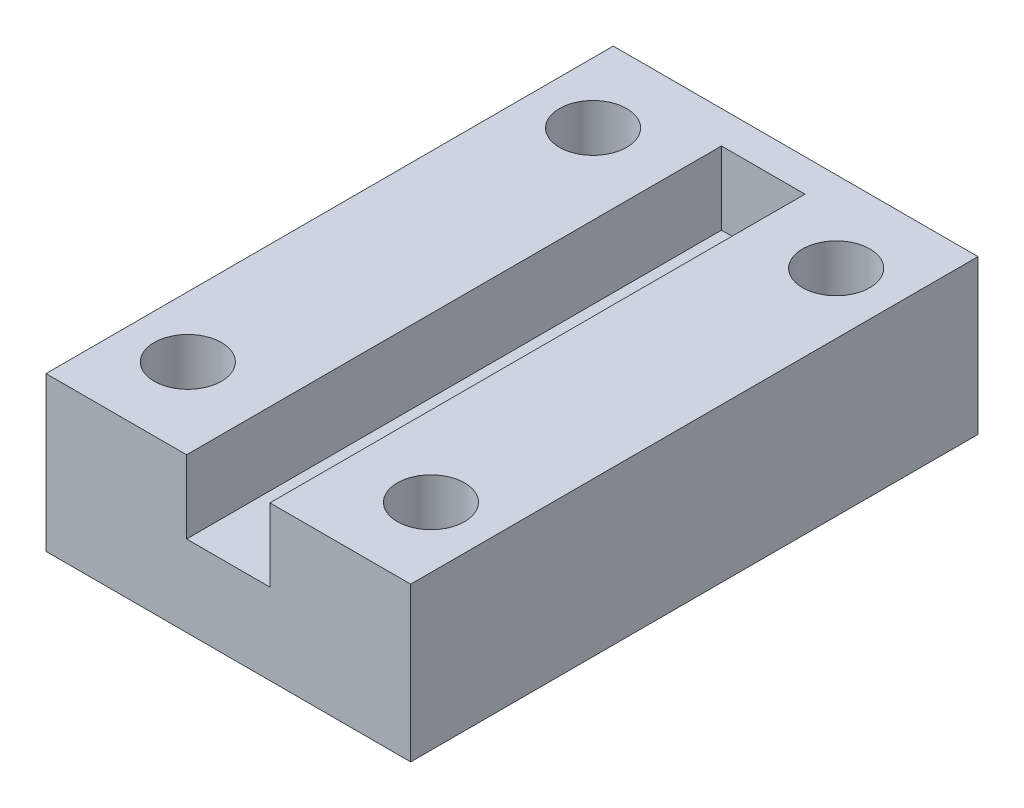
SolidWorks part; units mm, degrees
ref_plane "Спереди" through (0, 0, 0) normal (0, 0, 1) x (1, 0, 0)
ref_plane "Сверху" through (0, 0, 0) normal (0, 1, 0) x (1, 0, 0)
ref_plane "Справа" through (0, 0, 0) normal (1, 0, 0) x (0, 0, -1)
sketch "Sketch1" plane through (0, 0, 0) normal (0, 1, 0) x (1, 0, 0)
  line L1 (22.5, -35) -> (-22.5, -35)
  line L2 (22.5, -35) -> (22.5, 35)
  line L3 (22.5, 35) -> (-22.5, 35)
  line L4 (-22.5, -35) -> (-22.5, 35)
  line L5 (22.5, -35) -> (-22.5, 35) construction
  line L6 (22.5, 35) -> (-22.5, -35) construction
  point P0 (0, 0)
  dimension "D1" = 45
  dimension "D2" = 70
extrude "Boss-Extrude1" add sketch "Sketch1" along normal blind 10
sketch "Sketch3" plane through (0, 0, 0) normal (0, -1, 0) x (1, 0, 0)
  line L0 (15, -25) -> (15, 25) construction
  line L1 (-15, 25) -> (-15, -25) construction
  line L2 (-15, -25) -> (15, 25) construction
  line L3 (-22.5, -25) -> (22.5, -25) construction
  line L4 (-22.5, -35) -> (-22.5, 35) construction
  line L5 (22.5, 35) -> (22.5, -35) construction
  line L6 (-22.5, 25) -> (22.5, 25) construction
  line L7 (-22.5, -35) -> (-22.5, 35) construction
  line L8 (22.5, 35) -> (22.5, -35) construction
  line L9 (-15, 25) -> (15, -25) construction
  circle A0 centre (15, 25) radius 4.15
  circle A1 centre (15, -25) radius 4.15
  circle A2 centre (-15, -25) radius 4.15
  circle A3 centre (-15, 25) radius 4.15
  point P4 (0, 0)
  dimension "D1" = 8.3
  dimension "D2" = 30
  dimension "D3" = 50
extrude "Cut-Extrude2" cut sketch "Sketch3" against normal through all
sketch "Sketch5" plane through (0, 10, 0) normal (0, 1, 0) x (1, 0, 0)
  line L0 (5.15, 35) -> (-5.15, -35) construction
  line L1 (-5.15, -35) -> (-22.5, -35)
  line L2 (-5.15, -35) -> (-5.15, 35) construction
  line L3 (-5.15, 35) -> (-22.5, 35) construction
  line L4 (-22.5, -35) -> (-22.5, 35)
  line L5 (-5.15, -35) -> (-22.5, 35) construction
  line L6 (-5.15, 35) -> (-22.5, -35) construction
  line L7 (5.15, -35) -> (22.5, -35)
  line L8 (5.15, -35) -> (5.15, 35) construction
  line L9 (5.15, 35) -> (22.5, 35) construction
  line L10 (22.5, -35) -> (22.5, 35)
  line L11 (5.15, -35) -> (22.5, 35) construction
  line L12 (5.15, 35) -> (22.5, -35) construction
  line L13 (5.15, -35) -> (-5.15, 35) construction
  line L14 (-5.15, -35) -> (-5.15, 31)
  line L15 (-5.15, 31) -> (5.15, 31)
  line L16 (5.15, 31) -> (5.1302, -34.9493)
  line L17 (5.15, -35) -> (5.1302, -34.9493)
  line L18 (-22.5, 35) -> (22.5, 35)
  circle A0 centre (-15, 25) radius 4.15
  circle A1 centre (15, 25) radius 4.15
  circle A2 centre (15, -25) radius 4.15
  circle A3 centre (-15, -25) radius 4.15
  point P0 (-13.825, 0)
  point P6 (13.825, 0)
  point P12 (0, 0)
  dimension "D1" = 10.3
  dimension "D2" = 4
extrude "Boss-Extrude2" add sketch "Sketch5" along normal blind 9
chamfer "Chamfer1" distance 1 angle 50 4 edges at (15, 0, 20.85) (-15, 0, 20.85) (-15, 0, -29.15) (15, 0, -29.15)
